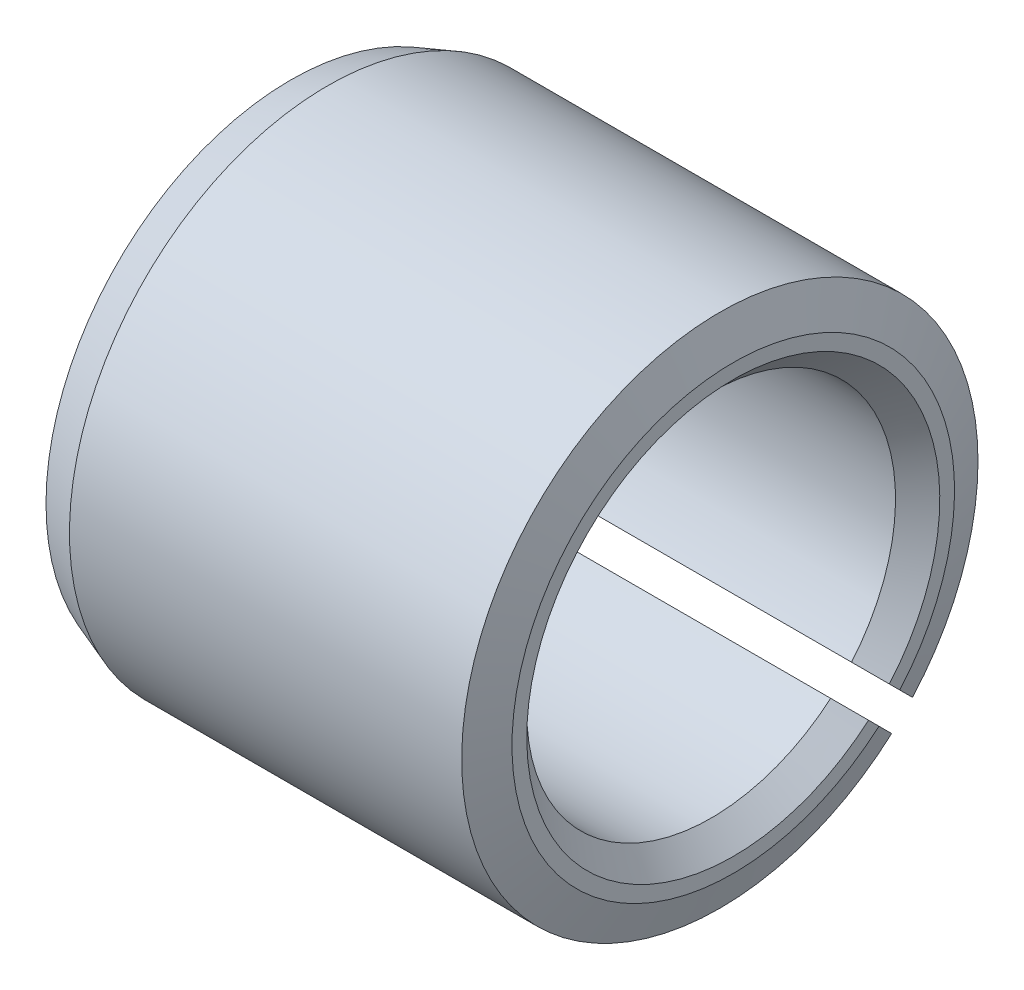
SolidWorks part; units mm, degrees
ref_plane "Front" through (0, 0, 0) normal (0, 0, 1) x (1, 0, 0)
ref_plane "Top" through (0, 0, 0) normal (0, 1, 0) x (1, 0, 0)
ref_plane "Right" through (0, 0, 0) normal (1, 0, 0) x (0, 0, -1)
sketch "Sketch1" plane through (0, 0, 0) normal (0, 0, 1) x (1, 0, 0)
  line L0 (0, 3.5) -> (0, 0)
  line L1 (0, 0) -> (6, 0)
  line L2 (6, 0) -> (6, 3.5)
  line L3 (6, 3.5) -> (0, 3.5)
  line L4 (0, 0) -> (6, 0) construction
revolve "Revolve1" add sketch "Sketch1" angle 360 about L4
sketch "Sketch2" plane through (0, 0, 0) normal (-1, 0, 0) x (0, 0, 1)
  line L0 (-2.3294, -2.6123) -> (-1.6207, -1.9035)
  line L1 (-1.9035, -1.6207) -> (-2.6123, -2.3294)
  arc A0 (-2.6123, -2.3294) -> (-2.3294, -2.6123) centre (0, 0) ccw
  arc A1 (-1.6207, -1.9035) -> (-1.9035, -1.6207) centre (0, 0) cw
extrude "Cut-Extrude1" cut sketch "Sketch2" against normal through all
sketch "Sketch3" plane through (0, 0, 0) normal (0, 0, 1) x (1, 0, 0)
  line L0 (0, 2.5) -> (0, 0)
  line L1 (0, 0) -> (6, 0)
  line L2 (6, 0) -> (6, 2.5)
  line L3 (6, 2.5) -> (0, 2.5)
  line L4 (0, 0) -> (6, 0) construction
revolve "Cut-Revolve1" cut sketch "Sketch3" angle 360 about L4
chamfer "Chamfer1" distance 0.3 angle 45 2 edges at (6, 1.7678, 1.7678) (0, 1.7678, 1.7678)
chamfer "Chamfer2" distance 0.182 angle 70 2 edges at (6, 2.4749, 2.4749) (0, 2.4749, 2.4749)
